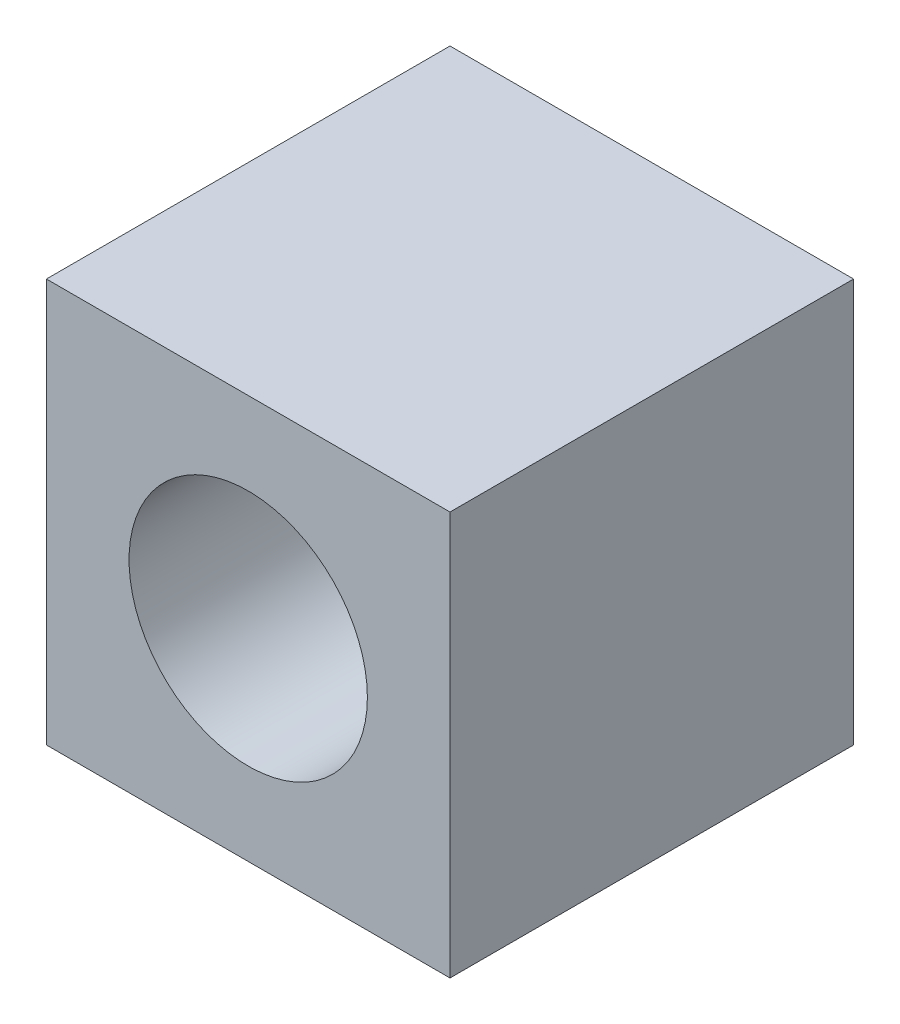
SolidWorks part; units mm, degrees
ref_plane "Front Plane" through (0, 0, 0) normal (0, 0, 1) x (1, 0, 0)
ref_plane "Top Plane" through (0, 0, 0) normal (0, 1, 0) x (1, 0, 0)
ref_plane "Right Plane" through (0, 0, 0) normal (1, 0, 0) x (0, 0, -1)
sketch "Sketch1" plane through (0, 0, 0) normal (0, 0, 1) x (1, 0, 0)
  line L1 (-25.4, 25.4) -> (25.4, 25.4)
  line L2 (-25.4, 25.4) -> (-25.4, -25.4)
  line L3 (-25.4, -25.4) -> (25.4, -25.4)
  line L4 (25.4, 25.4) -> (25.4, -25.4)
  line L5 (-25.4, 25.4) -> (25.4, -25.4) construction
  line L6 (-25.4, -25.4) -> (25.4, 25.4) construction
  point P0 (0, 0)
  dimension "D1" = 50.8
  dimension "D2" = 50.8
extrude "Boss-Extrude1" add sketch "Sketch1" along normal blind 50.8
sketch "Sketch2" plane through (0, 0, 50.8) normal (0, 0, 1) x (1, 0, 0)
  circle A0 centre (0, 0) radius 15
  dimension "D1" = 30
extrude "Cut-Extrude1" cut sketch "Sketch2" against normal blind 50.8
